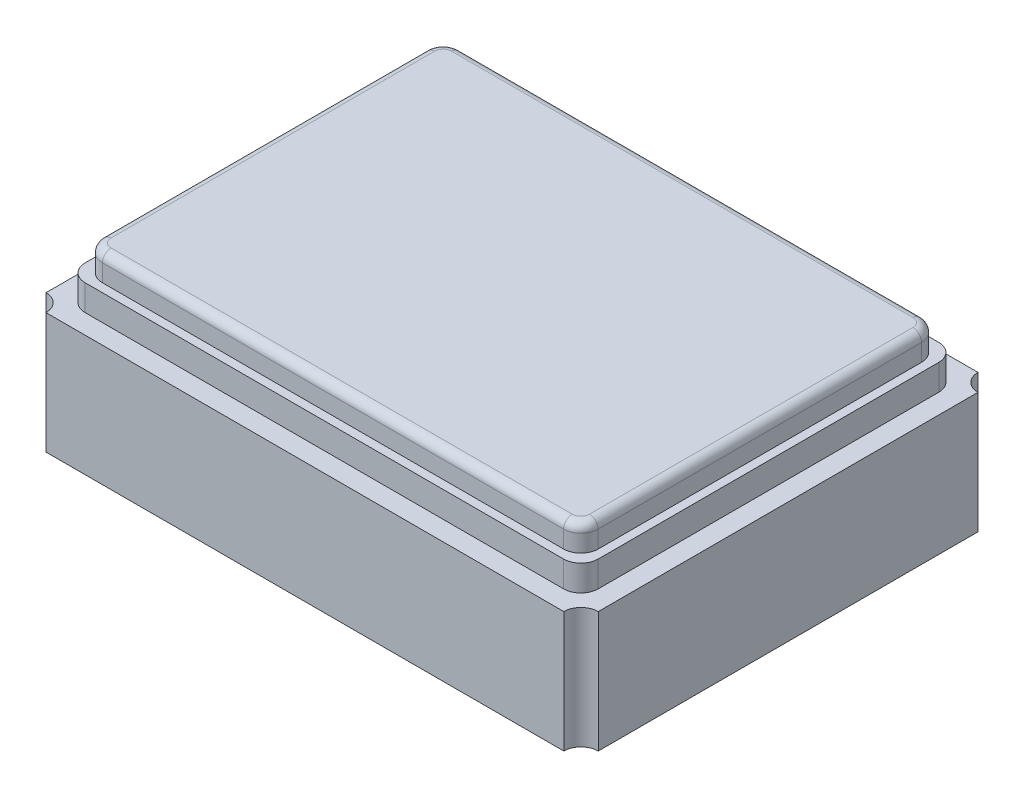
SolidWorks part; units mm, degrees
ref_plane "Front Plane" through (0, 0, 0) normal (0, 0, 1) x (1, 0, 0)
ref_plane "Top Plane" through (0, 0, 0) normal (0, 1, 0) x (1, 0, 0)
ref_plane "Right Plane" through (0, 0, 0) normal (1, 0, 0) x (0, 0, -1)
sketch "Sketch1" plane through (0, 0, 0) normal (0, 1, 0) x (1, 0, 0)
  line L1 (-1.6, -1.2) -> (1.6, -1.2)
  line L2 (-1.6, -1.2) -> (-1.6, 1.2)
  line L3 (-1.6, 1.2) -> (1.6, 1.2)
  line L4 (1.6, -1.2) -> (1.6, 1.2)
  line L5 (-1.6, -1.2) -> (1.6, 1.2) construction
  line L6 (-1.6, 1.2) -> (1.6, -1.2) construction
  point P0 (0, 0)
  dimension "D1" = 3.2
  dimension "D2" = 2.4
extrude "Boss-Extrude1" add sketch "Sketch1" along normal blind 0.7
sketch "Sketch2" plane through (0, 0.7, 0) normal (0, 1, 0) x (1, 0, 0)
  circle A0 centre (-1.6, 1.2) radius 0.1
  circle A1 centre (1.6, 1.2) radius 0.1
  circle A2 centre (1.6, -1.2) radius 0.1
  circle A3 centre (-1.6, -1.2) radius 0.1
extrude "Cut-Extrude1" cut sketch "Sketch2" against normal through all
sketch "Sketch3" plane through (0, 0.7, 0) normal (0, 1, 0) x (1, 0, 0)
  line L1 (-1.3861, -1.0868) -> (1.3861, -1.0868)
  line L2 (-1.4861, -0.9868) -> (-1.4861, 0.9868)
  line L3 (-1.3861, 1.0868) -> (1.3861, 1.0868)
  line L4 (1.4861, -0.9868) -> (1.4861, 0.9868)
  line L5 (-1.4861, -1.0868) -> (1.4861, 1.0868) construction
  line L6 (-1.4861, 1.0868) -> (1.4861, -1.0868) construction
  arc A0 (-1.3861, -1.0868) -> (-1.4861, -0.9868) centre (-1.3861, -0.9868) cw
  arc A1 (1.3861, -1.0868) -> (1.4861, -0.9868) centre (1.3861, -0.9868) ccw
  arc A2 (1.3861, 1.0868) -> (1.4861, 0.9868) centre (1.3861, 0.9868) cw
  arc A3 (-1.4861, 0.9868) -> (-1.3861, 1.0868) centre (-1.3861, 0.9868) cw
  point P0 (0, 0)
  dimension "D1" = 0.1
extrude "Boss-Extrude2" add sketch "Sketch3" along normal blind 0.15 separate body
sketch "Sketch4" plane through (0, 0.85, 0) normal (0, 1, 0) x (1, 0, 0)
  line L8 (-1.3861, -1.0368) -> (1.3861, -1.0368)
  line L9 (1.4361, -0.9868) -> (1.4361, 0.9868)
  line L10 (1.3861, 1.0368) -> (-1.3861, 1.0368)
  line L11 (-1.4361, 0.9868) -> (-1.4361, -0.9868)
  line L12 (-1.3361, -1.0368) -> (1.3361, -1.0368)
  line L13 (1.4361, -0.9368) -> (1.4361, 0.9368)
  line L14 (1.3361, 1.0368) -> (-1.3361, 1.0368)
  line L15 (-1.4361, 0.9368) -> (-1.4361, -0.9368)
  arc A4 (-1.3361, -1.0368) -> (-1.4361, -0.9368) centre (-1.3361, -0.9368) cw
  arc A5 (1.3361, -1.0368) -> (1.4361, -0.9368) centre (1.3361, -0.9368) ccw
  arc A6 (1.4361, 0.9368) -> (1.3361, 1.0368) centre (1.3361, 0.9368) ccw
  arc A7 (-1.3361, 1.0368) -> (-1.4361, 0.9368) centre (-1.3361, 0.9368) ccw
  arc A12 (-1.4361, -0.9868) -> (-1.3861, -1.0368) centre (-1.3861, -0.9868) ccw
  arc A14 (1.3861, -1.0368) -> (1.4361, -0.9868) centre (1.3861, -0.9868) ccw
  arc A16 (1.4361, 0.9868) -> (1.3861, 1.0368) centre (1.3861, 0.9868) ccw
  arc A18 (-1.3861, 1.0368) -> (-1.4361, 0.9868) centre (-1.3861, 0.9868) ccw
  dimension "D2" = 0.1
  dimension "D1" = 0.05
extrude "Boss-Extrude3" add sketch "Sketch4" along normal blind 0.15 separate body
fillet "Fillet1" radius 0.05 8 edges at (-1.4361, 1, 0) (-1.4068, 1, -1.0076) (0, 1, -1.0368) (1.4068, 1, -1.0076) (1.4361, 1, 0) (1.4068, 1, 1.0076) (0, 1, 1.0368) (-1.4068, 1, 1.0076)
